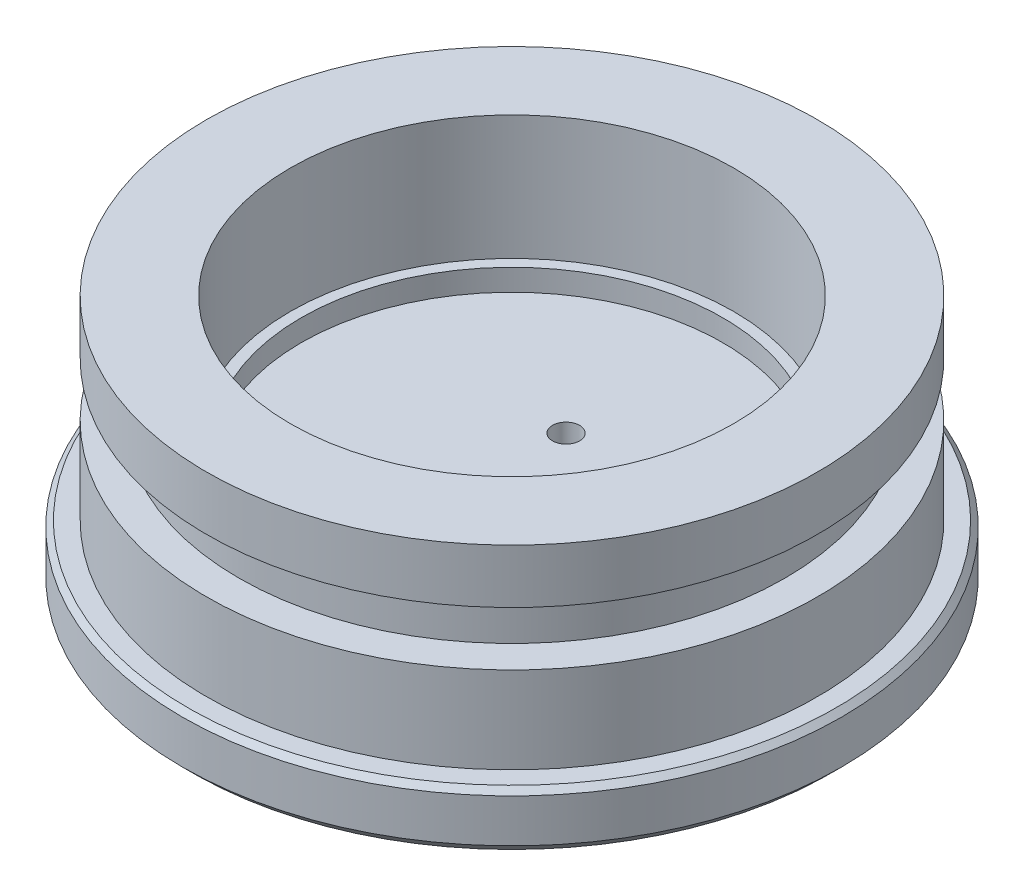
SolidWorks part; units mm, degrees
material "Delrin 2700 NC010, Ацеталь сополимер низкой вязкости (SS)"
ref_plane "Спереди" through (0, 0, 0) normal (0, 0, 1) x (1, 0, 0)
ref_plane "Сверху" through (0, 0, 0) normal (0, 1, 0) x (1, 0, 0)
ref_plane "Справа" through (0, 0, 0) normal (1, 0, 0) x (0, 0, -1)
sketch "Эскиз1" plane through (0, 0, 0) normal (0, 0, 1) x (1, 0, 0)
  line L0 (0, 0) -> (-29.5, 0)
  line L1 (-29.5, 0) -> (-30.5, 1)
  line L2 (-30.5, 1) -> (-30.5, 5)
  line L3 (-30.5, 5) -> (-30, 5.5)
  line L4 (-30, 5.5) -> (-28.25, 5.5)
  line L5 (-28.25, 5.5) -> (-28.25, 13.5)
  line L6 (-28.25, 13.5) -> (-25.25, 13.5)
  line L7 (-25.25, 13.5) -> (-25.25, 18.5)
  line L8 (-25.25, 18.5) -> (-28.25, 18.5)
  line L9 (-28.25, 18.5) -> (-28.25, 23.5)
  line L10 (-28.25, 23.5) -> (-20.5, 23.5)
  line L11 (-20.5, 23.5) -> (-20.5, 12)
  line L12 (-19.5, 12) -> (-19.5, 10)
  line L13 (0, 10) -> (0, 0)
  line L14 (-20.5, 12) -> (-19.5, 12)
  line L15 (-19.5, 10) -> (0, 10)
  point P22 (-20, 12)
  dimension "D1" = 1
  dimension "D2" = 30.5
  dimension "D3" = 0.5
  dimension "D4" = 28.25
  dimension "D5" = 20.5
  dimension "D6" = 2
  dimension "D7" = 10
revolve "Повернуть1" add sketch "Эскиз1" angle 360 about L13
sketch "Эскиз2" plane through (0, 10, 0) normal (0, 1, 0) x (1, 0, 0)
  circle A0 centre (0, 5) radius 1.75
hole_wizard "Отверстие обработанное метчиком M3x0.51" positions "Трехмерный эскиз1" profile "Эскиз3" tap size "M3x0.5" standard "Ansi Metric"
sketch3d "Трехмерный эскиз1"
  point P0 (0, 10, -5)
sketch "Эскиз3" plane through (0, 10, -5) normal (1, 0, 0) x (0, 0, 1)
  line L0 (0, 0) -> (0, 7.7511)
  line L1 (0, 7.7511) -> (1.25, 7)
  line L2 (1.25, 7) -> (1.25, 0)
  line L5 (1.25, 0) -> (0, 0)
  line L10 (0, 7.7511) -> (-1.25, 7) construction
  line L11 (0, -6.35) -> (0, 107.95) construction
  dimension "Диаметр сверла" = 2.5
  dimension "Глубина сверла" = 7
  dimension "Угол заточки сверла" = 118
cosmetic thread "Отверстие резьбы1" parameters "D1"=6, "D2"=3
